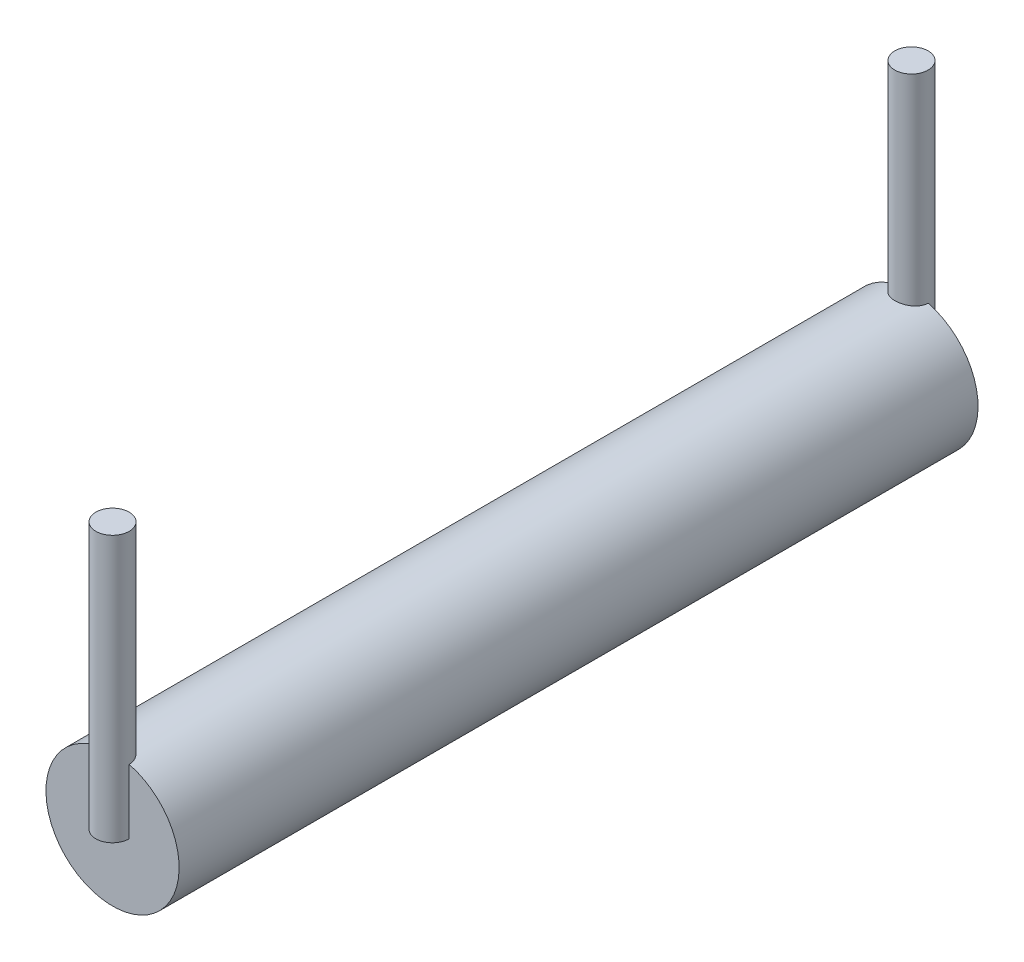
SolidWorks part; units mm, degrees
ref_plane "Front Plane" through (0, 0, 0) normal (0, 0, 1) x (1, 0, 0)
ref_plane "Top Plane" through (0, 0, 0) normal (0, 1, 0) x (1, 0, 0)
ref_plane "Right Plane" through (0, 0, 0) normal (1, 0, 0) x (0, 0, -1)
sketch "Sketch1" plane through (0, 0, 0) normal (0, 0, 1) x (1, 0, 0)
  circle A0 centre (0, 0) radius 1
  dimension "D1" = 2
extrude "Boss-Extrude1" add sketch "Sketch1" along normal mid plane 12
sketch "Sketch2" plane through (0, 0, 0) normal (0, 1, 0) x (1, 0, 0)
  line L0 (-1, -6) -> (1, -6) construction
  line L1 (1, 6) -> (-1, 6) construction
  circle A0 centre (0, -6) radius 0.25
  circle A1 centre (0, 6) radius 0.25
  dimension "D1" = 0.5
  dimension "D2" = 0.5
extrude "Boss-Extrude2" add sketch "Sketch2" along normal blind 4
